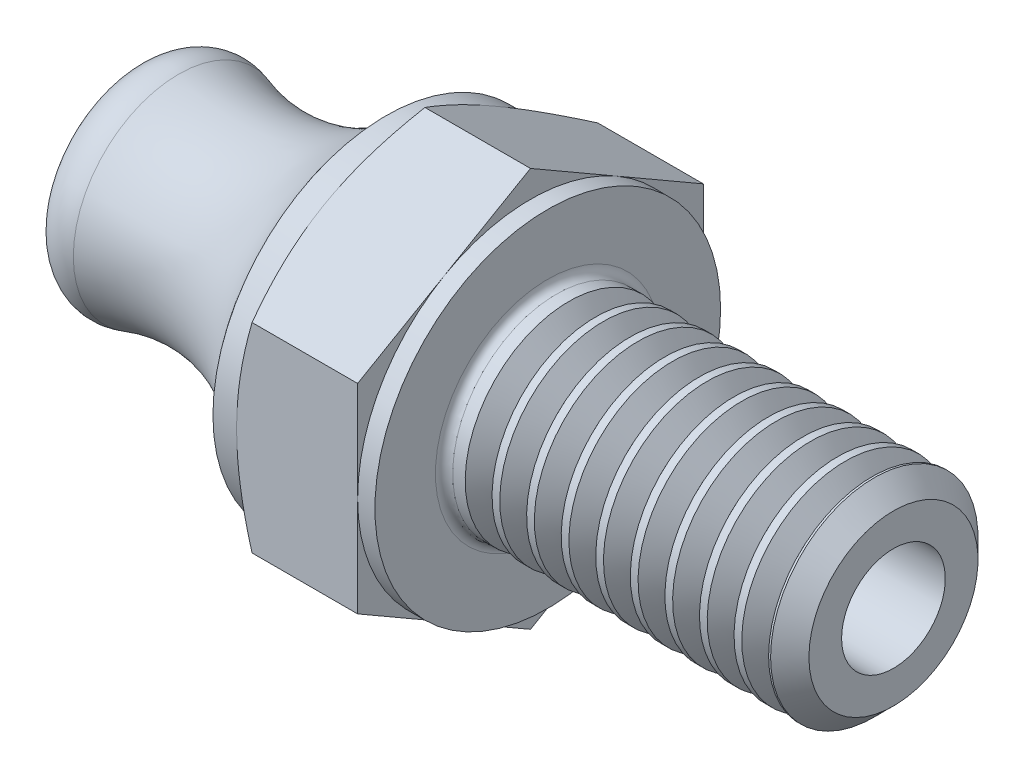
SolidWorks part; units mm, degrees
ref_plane "Plane1" through (0, 0, 0) normal (0, 0, 1) x (1, 0, 0)
ref_plane "Plane2" through (0, 0, 0) normal (0, 1, 0) x (1, 0, 0)
ref_plane "Plane3" through (0, 0, 0) normal (1, 0, 0) x (0, 0, -1)
sketch "Sketch1" plane through (0, 0, 0) normal (1, 0, 0) x (0, 0, -1)
  line L0 (5, 2.8868) -> (5, -2.8868)
  line L1 (-5, 2.8868) -> (-5, -2.8868)
  line L2 (5, -2.8868) -> (0, -5.7735)
  line L3 (0, -5.7735) -> (-5, -2.8868)
  line L4 (5, 2.8868) -> (0, 5.7735)
  line L5 (0, 5.7735) -> (-5, 2.8868)
  dimension "Width_flats" = 10
  dimension "D2" = 120
  dimension "D3" = 5
  dimension "D4" = 5
  dimension "D5" = 5
extrude "BaseHead" add sketch "Sketch1" along normal blind 4
sketch "BodySke" plane through (0, 0, 0) normal (0, 0, 1) x (1, 0, 0)
  line L0 (0, 2.8868) -> (0, -2.8868) construction
  line L1 (0, 0) -> (14, 0)
  line L2 (0, 0) -> (0, 3)
  line L3 (0, 3) -> (13.4455, 3)
  line L4 (14, 0) -> (14, 2.4455)
  line L5 (4, 5.7735) -> (4, 2.8868) construction
  line L6 (14, 2.4455) -> (13.4455, 3)
  line L7 (0, 0) -> (96.52, 0) construction
  line L8 (14, -2.4455) -> (13.4455, -3) construction
  line L9 (0, -3) -> (13.4455, -3) construction
  line L10 (5, 15.24) -> (5, -1.27) construction
  line L11 (-16, 15.24) -> (-16, -1.27) construction
  line L12 (4, 2.8868) -> (4, -2.8868) construction
  dimension "Length" = 10
  dimension "Body_ch_ang" = 45
  dimension "Diameter" = 6
  dimension "Minor_dia" = 4.891
  dimension "Advance" = 1
  dimension "Thread_nom" = 30
revolve "BaseBody" add sketch "BodySke"
cosmetic thread "ThreadCosmetic" [suppressed]
fillet "HeadFillet" radius 0.25 1 edges at (4, 0, -3)
sketch "Sketch3" plane through (0, 0, 0) normal (0, 0, 1) x (1, 0, 0)
  line L0 (0, 5) -> (3.3333, 10.7735)
  line L1 (0, 5.7735) -> (0, 2.8868) construction
  line L2 (3.3333, 10.7735) -> (3.3333, 15.7735)
  line L3 (3.3333, 15.7735) -> (-10, 15.7735)
  line L4 (-10, 15.7735) -> (-10, 5)
  line L5 (-10, 5) -> (0, 5)
  line L6 (0, 0) -> (99.06, 0) construction
  line L7 (4, 5.7735) -> (0, 5.7735) construction
  dimension "D1" = 5
  dimension "D2" = 5
  dimension "D3" = 10
  dimension "D4" = 5
  dimension "Head_ch_ang" = 30
revolve "HeadChamfer" cut sketch "Sketch3" angle 360 about L6
sketch "Sketch4" plane through (0, 0, 0) normal (0, 0, 1) x (1, 0, 0)
  line L1 (4, 5.7735) -> (4, 2.8868) construction
  line L2 (4, 5) -> (3.5, 5)
  line L3 (4, 5) -> (4, 15.7735)
  line L4 (4, 15.7735) -> (3.5, 15.7735)
  line L5 (0, 0) -> (95.25, 0) construction
  line L6 (0, 0) -> (96.52, 0) construction
  line L7 (3.5, 5) -> (3.5, 15.7735)
  line L8 (4, 5.7735) -> (0.4466, 5.7735) construction
  dimension "D1" = 10
  dimension "D2" = 10
  dimension "Bearing_ht" = 0.5
revolve "BearingFace" cut sketch "Sketch4" angle 360 about L5
sketch "ThdSchSke" plane through (0, 0, 0) normal (0, 0, 1) x (1, 0, 0)
  line L0 (5, -2.4455) -> (4.6117, -3)
  line L1 (5, -2.4455) -> (5.3883, -3)
  line L2 (5.3883, -3) -> (5.3883, -3.75)
  line L3 (-3.175, 0) -> (5.1513, 0) construction
  line L5 (5.3883, -3.75) -> (4.6117, -3.75)
  line L6 (4.6117, -3.75) -> (4.6117, -3)
  dimension "Thread_minor" = 4.891
  dimension "Diameter" = 6
  dimension "Start" = 5
  dimension "SideAngle" = 55
  dimension "VeeAngle" = 70
  dimension "Overcut" = 7.5
revolve "ThreadSchematic" cut sketch "ThdSchSke" angle 360 about L3
pattern_linear "ThdSchPat" count 9 spacing 1 along (1, 0, 0) of "ThreadSchematic"
sketch "Sketch8" plane through (0, 0, 0) normal (-1, 0, 0) x (0, 0, 1)
  circle A0 centre (0, 0) radius 5
extrude "Boss-Extrude3" add sketch "Sketch8" along normal blind 8
sketch "Sketch9" plane through (-8, 0, 0) normal (-1, 0, 0) x (0, 0, 1)
  circle A0 centre (0, 0) radius 1.5
  dimension "D1" = 3
extrude "Cut-Extrude2" cut sketch "Sketch9" against normal blind 48
sketch "Sketch10" plane through (0, 0, 0) normal (0, 0, 1) x (1, 0, 0)
  line L0 (0, 5) -> (-8, 5) construction
  line L1 (-8, 5) -> (-8, -5) construction
  line L2 (-0.6854, 5) -> (-8, 5)
  line L3 (-8, 5) -> (-8, 3.7189)
  arc A0 (-0.6854, 5) -> (-8, 3.7189) centre (-4.9832, 8.0168) cw
revolve "Cut-Revolve1" cut sketch "Sketch10" angle 360 about axis through (-8, 0, 0) along (1, 0, 0)
fillet "Fillet1" radius 1 1 edges at (-8, 0, 3.7189)
